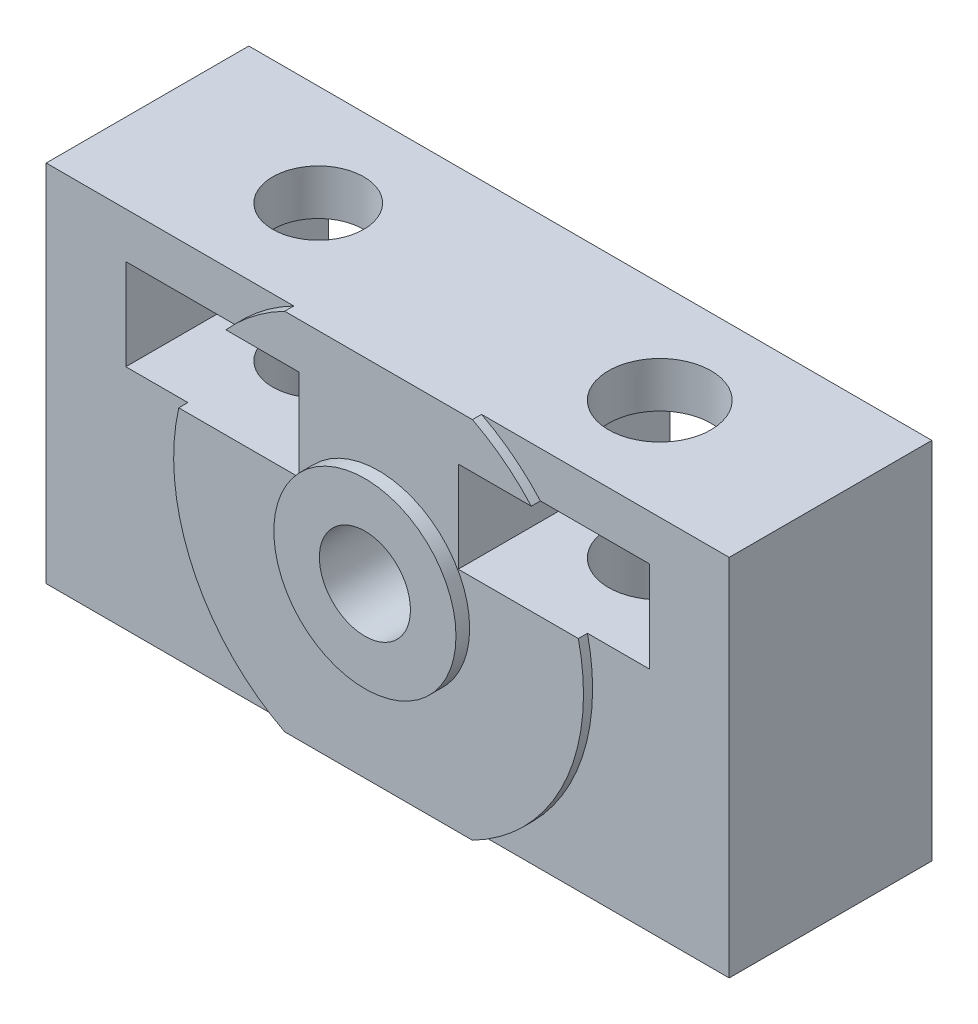
SolidWorks part; units mm, degrees
material "ABS"
ref_plane "Спереди" through (0, 0, 0) normal (0, 0, 1) x (1, 0, 0)
ref_plane "Сверху" through (0, 0, 0) normal (0, 1, 0) x (1, 0, 0)
ref_plane "Справа" through (0, 0, 0) normal (1, 0, 0) x (0, 0, -1)
sketch "Эскиз1" plane through (0, 0, 0) normal (0, 0, 1) x (1, 0, 0)
  line L1 (15, -8) -> (-15, -8)
  line L2 (15, -8) -> (15, 8)
  line L3 (15, 8) -> (-15, 8)
  line L4 (-15, -8) -> (-15, 8)
  line L5 (15, -8) -> (-15, 8) construction
  line L6 (15, 8) -> (-15, -8) construction
  circle A0 centre (0, 0) radius 2
  point P0 (0, 0)
  dimension "D3" = 4
  dimension "D1" = 30
  dimension "D2" = 16
extrude "Бобышка-Вытянуть1" add sketch "Эскиз1" along normal blind 8.9
ref_plane "Плоскость1" through (0, 0, 0) normal (0, 1, 0) x (-1, 0, 0)
sketch "Эскиз5" plane through (0, 0, 0) normal (0, 1, 0) x (-1, 0, 0)
  line L0 (2, 8.9) -> (2, 9.9)
  line L1 (2, 9.9) -> (4, 9.9)
  line L2 (15, 8.9) -> (-15, 8.9) construction
  line L3 (9, 8.9) -> (2, 8.9)
  line L4 (4, 9.9) -> (4, 9.3)
  line L5 (0, 8.9) -> (0, 0) construction
  line L6 (15, 0) -> (-15, 0) construction
  line L7 (4, 9.3) -> (9, 9.3)
  line L8 (9, 9.3) -> (9, 8.9)
  dimension "D1" = 1
  dimension "D2" = 0.6
  dimension "D3" = 2
  dimension "D4" = 9
revolve "Повернуть1" add sketch "Эскиз5" angle 360 about L5
sketch "Эскиз2" plane through (0, -8, 0) normal (0, -1, 0) x (1, 0, 0)
  line L0 (-15, 4.45) -> (0, 4.45) construction
  line L1 (-15, 8.9) -> (-15, 0) construction
  line L2 (0, 4.45) -> (0, 8.9) construction
  line L3 (-4.1231, 8.9) -> (4.1231, 8.9) construction
  line L5 (15, 8.9) -> (15, 0) construction
  line L6 (15, 4.45) -> (0, 4.45) construction
  circle A0 centre (-7.5, 4.45) radius 2
  circle A1 centre (7.5, 4.45) radius 2.25
  dimension "D1" = 4.5
  dimension "D2" = 4
extrude "Вырез-Вытянуть1" cut sketch "Эскиз2" against normal through all
sketch "Эскиз3" plane through (0, 0, 8.9) normal (0, 0, 1) x (1, 0, 0)
  line L0 (-15, 4) -> (0, 4) construction
  line L1 (15, 8) -> (4.1231, 8) construction
  line L2 (0, 4) -> (15, 4) construction
  line L4 (0, 8) -> (0, 4) construction
  line L5 (-3.5, 2) -> (-11.5, 2)
  line L6 (-3.5, 2) -> (-3.5, 6)
  line L7 (-3.5, 6) -> (-11.5, 6)
  line L8 (-11.5, 2) -> (-11.5, 6)
  line L9 (-3.5, 2) -> (-11.5, 6) construction
  line L10 (-3.5, 6) -> (-11.5, 2) construction
  line L11 (11.5, 2) -> (3.5, 2)
  line L12 (11.5, 2) -> (11.5, 6)
  line L13 (11.5, 6) -> (3.5, 6)
  line L14 (3.5, 2) -> (3.5, 6)
  line L15 (11.5, 2) -> (3.5, 6) construction
  line L16 (11.5, 6) -> (3.5, 2) construction
  line L18 (0, 4) -> (0, 0) construction
  line L19 (-15, 8) -> (-15, -8) construction
  line L20 (15, -8) -> (15, 8) construction
  point P8 (-7.5, 4)
  point P13 (7.5, 4)
  dimension "D1" = 8
  dimension "D2" = 4
extrude "Вырез-Вытянуть2" cut sketch "Эскиз3" against normal through all and the other way through all
sketch "Эскиз7" plane through (0, 0, 0) normal (0, 0, -1) x (-1, 0, 0)
  line L1 (4.1231, -8) -> (-4.1231, -8)
  line L2 (4.1231, -8) -> (4.1231, 8)
  line L3 (4.1231, 8) -> (-4.1231, 8)
  line L4 (-4.1231, -8) -> (-4.1231, 8)
  line L5 (4.1231, -8) -> (-4.1231, 8) construction
  line L6 (4.1231, 8) -> (-4.1231, -8) construction
  circle A0 centre (0, 0) radius 9
  line M16 (15, 8) -> (-15, 8)
  line M18 (-15, -8) -> (15, -8)
extrude "Вырез-Вытянуть4" cut sketch "Эскиз7" against normal through all contours A0 M16 | A0 M18
